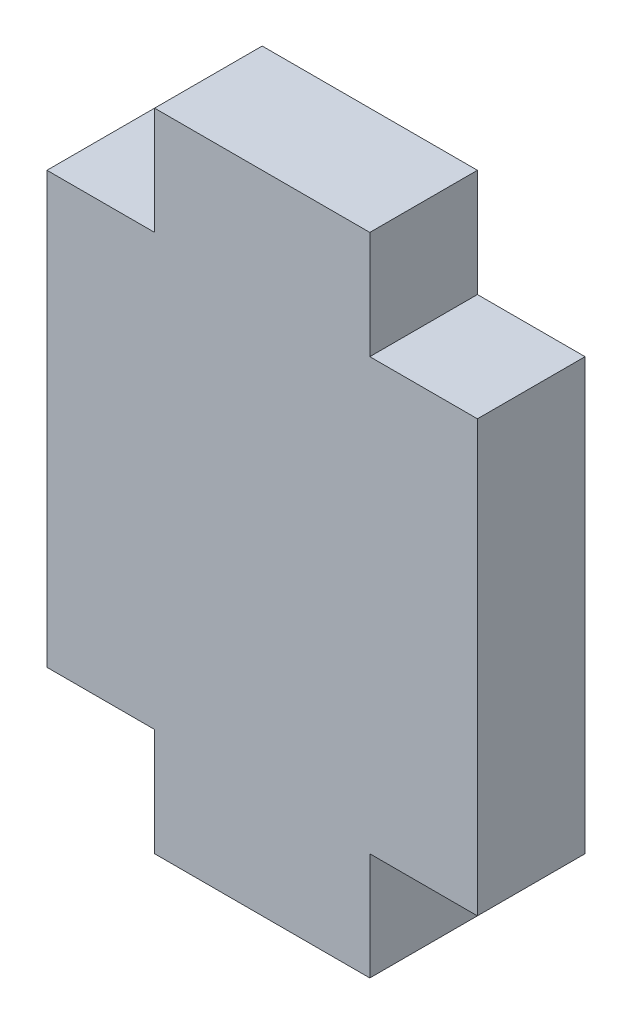
SolidWorks part; units mm, degrees
ref_plane "Front Plane" through (0, 0, 0) normal (0, 0, 1) x (1, 0, 0)
ref_plane "Top Plane" through (0, 0, 0) normal (0, 1, 0) x (1, 0, 0)
ref_plane "Right Plane" through (0, 0, 0) normal (1, 0, 0) x (0, 0, -1)
sketch "Sketch1" plane through (0, 0, 0) normal (0, 0, 1) x (1, 0, 0)
  line L0 (-12.7, 0) -> (-12.7, 25.4) construction
  line L1 (0, 0) -> (-6.35, 0)
  line L2 (0, 0) -> (0, 25.4)
  line L3 (0, 25.4) -> (-6.35, 25.4)
  line L4 (-25.4, 0) -> (-25.4, 25.4)
  line L5 (-12.7, 31.75) -> (-12.7, 25.4) construction
  line L6 (-19.05, 0) -> (-25.4, 0)
  line L7 (-19.05, 25.4) -> (-19.05, 31.75)
  line L8 (-19.05, 31.75) -> (-6.35, 31.75)
  line L9 (-6.35, 25.4) -> (-6.35, 31.75)
  line L10 (-25.4, 12.7) -> (0, 12.7) construction
  line L11 (-19.05, 25.4) -> (-25.4, 25.4)
  line L12 (-6.35, 0) -> (-6.35, -6.35)
  line L13 (-19.05, -6.35) -> (-6.35, -6.35)
  line L14 (0, 0) -> (-6.35, 0)
  line L15 (-12.7, -6.35) -> (-12.7, 0) construction
  line L16 (-19.05, 0) -> (-19.05, -6.35)
  line L17 (-19.05, 0) -> (-25.4, 0)
  dimension "D1" = 12.7
  dimension "D2" = 6.35
  dimension "D3" = 25.4
  dimension "D4" = 25.4
extrude "Boss-Extrude1" add sketch "Sketch1" along normal blind 6.35 contours L6 L16 L13 L12 L1 L2 L3 L9 L8 L7 L11 L4
